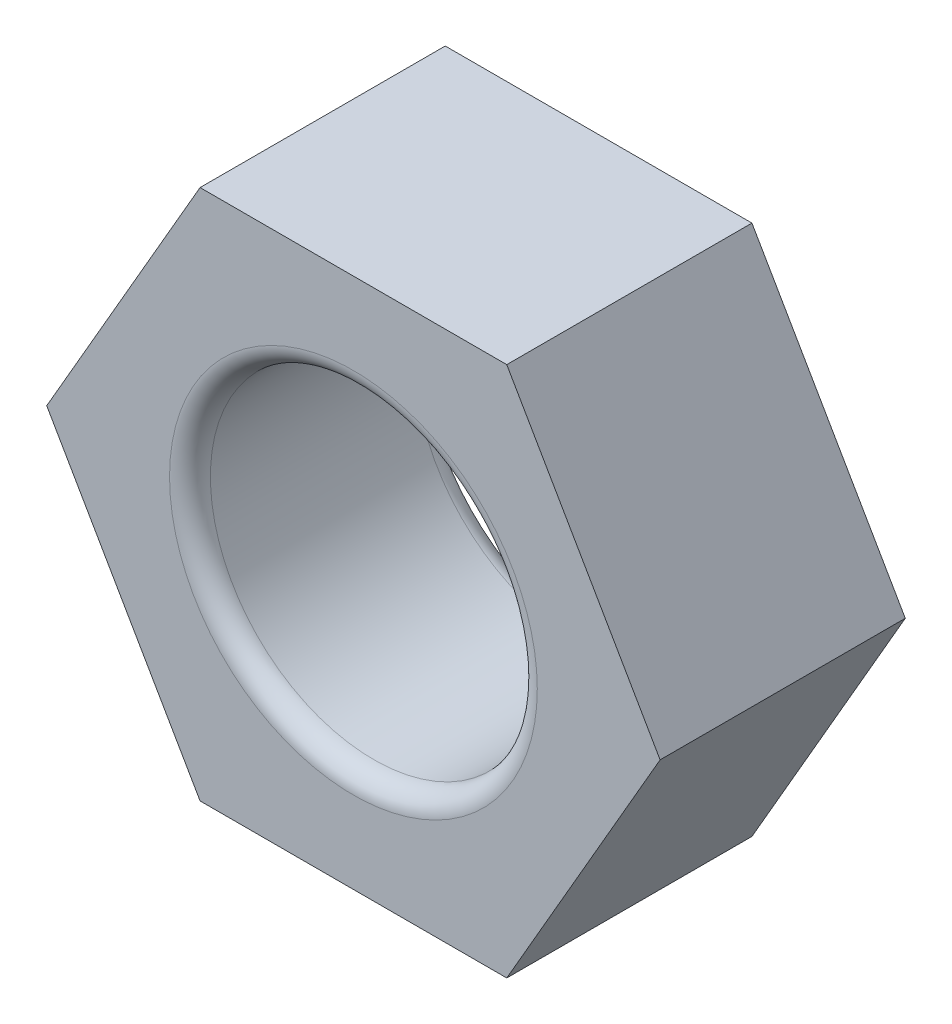
SolidWorks part; units mm, degrees
ref_plane "Plan de face" through (0, 0, 0) normal (0, 0, 1) x (1, 0, 0)
ref_plane "Plan de dessus" through (0, 0, 0) normal (0, 1, 0) x (1, 0, 0)
ref_plane "Plan de droite" through (0, 0, 0) normal (1, 0, 0) x (0, 0, -1)
sketch "Esquisse1" plane through (0, 0, 0) normal (0, 0, 1) x (1, 0, 0)
  line L0 (7.5056, 0) -> (3.7528, 6.5)
  line L1 (3.7528, 6.5) -> (-3.7528, 6.5)
  line L2 (3.7528, -6.5) -> (7.5056, 0)
  line L3 (-3.7528, -6.5) -> (3.7528, -6.5)
  line L4 (-7.5056, 0) -> (-3.7528, -6.5)
  line L5 (-3.7528, 6.5) -> (-7.5056, 0)
  circle A0 centre (0, 0) radius 4
extrude "Extrusion1" add sketch "Esquisse1" along normal blind 6
fillet "Congé1" radius 0.5 2 edges at (4, 0, 0) (4, 0, 6)
